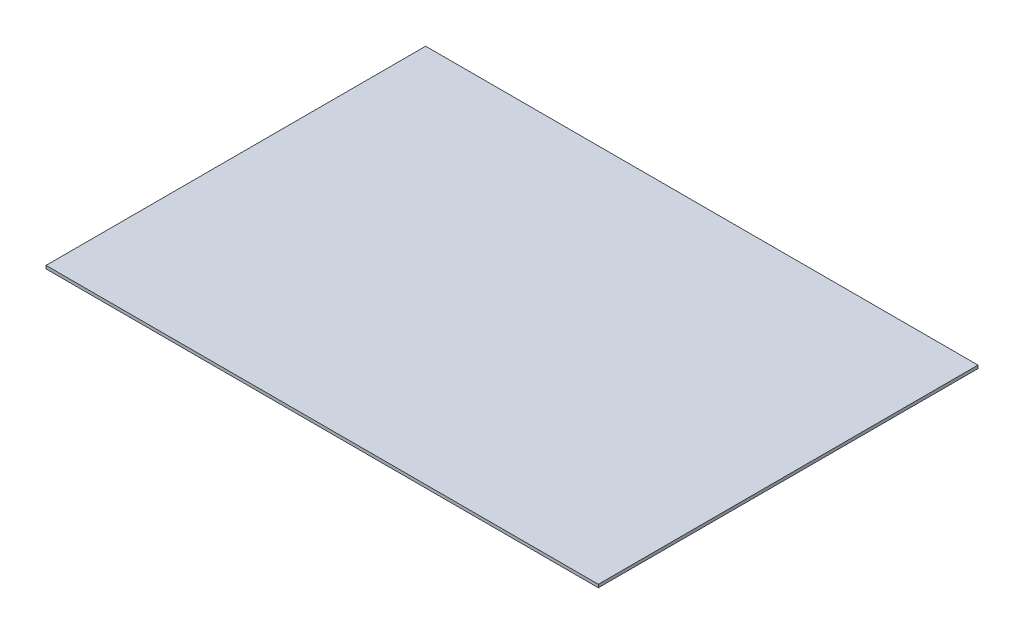
SolidWorks part; units mm, degrees
ref_plane "Front Plane" through (0, 0, 0) normal (0, 0, 1) x (1, 0, 0)
ref_plane "Top Plane" through (0, 0, 0) normal (0, 1, 0) x (1, 0, 0)
ref_plane "Right Plane" through (0, 0, 0) normal (1, 0, 0) x (0, 0, -1)
sketch "Sketch1" plane through (0, 0, 0) normal (0, 1, 0) x (1, 0, 0)
  line L1 (0, 0) -> (362.14, 0)
  line L2 (0, 0) -> (0, 248.92)
  line L3 (0, 248.92) -> (362.14, 248.92)
  line L4 (362.14, 0) -> (362.14, 248.92)
  dimension "D1" = 248.92
  dimension "D2" = 362.14
extrude "Boss-Extrude1" add sketch "Sketch1" along normal blind 2 contours L2 L3 L4 L1
sketch "Sketch2" plane through (0, 2, 0) normal (0, 1, 0) x (1, 0, 0)
  line L0 (77.2809, -416.6532) -> (35.0509, -416.6532) construction
  line L1 (94.503, -356.5138) -> (96.6486, -356.5138)
  line L2 (94.503, -356.5138) -> (94.503, 14144.4817)
  line L3 (94.503, 14144.4817) -> (96.6486, 14390.3473)
  line L4 (96.6486, -356.5138) -> (96.6486, 14390.3473)
  line L6 (33.6243, -273.1987) -> (-16.0257, -273.1987) construction
  line L9 (-42.9117, -455.7528) -> (-41.6638, -312.7583) construction
  dimension "D1" = 60.1394
  dimension "D2" = 70.3006
  dimension "D3" = 245.8749
  dimension "D4" = 10
